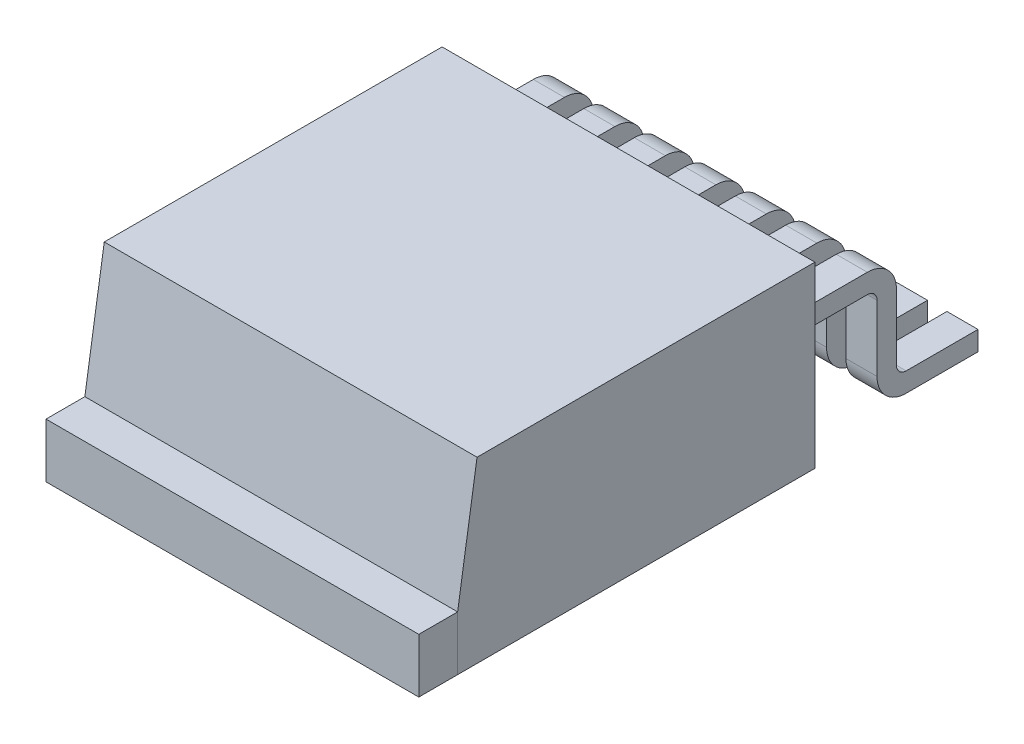
SolidWorks part; units mm, degrees
ref_plane "Front Plane" through (0, 0, 0) normal (0, 0, 1) x (1, 0, 0)
ref_plane "Top Plane" through (0, 0, 0) normal (0, 1, 0) x (1, 0, 0)
ref_plane "Right Plane" through (0, 0, 0) normal (1, 0, 0) x (0, 0, -1)
sketch "Sketch1" plane through (0, 0, 0) normal (1, 0, 0) x (0, 0, -1)
  line L0 (4.6, 0) -> (4.6, 4.6)
  line L1 (4.6, 4.6) -> (-4.1, 4.6)
  line L3 (-4.6, 0) -> (4.6, 0)
  line L4 (-4.1, 4.6) -> (-4.6, 1.4)
  line L5 (-4.6, 1.4) -> (-4.6, 0)
  dimension "D1" = 8.7
  dimension "D2" = 4.6
  dimension "D3" = 9.2
  dimension "D4" = 1.4
extrude "Boss-Extrude1" add sketch "Sketch1" along normal mid plane 9.6
sketch "Sketch2" plane through (0, 0, 4.6) normal (0, 0, 1) x (1, 0, 0)
  line L1 (4.8, 1.4) -> (-4.8, 1.4)
  line L2 (4.8, 1.4) -> (4.8, 0)
  line L3 (4.8, 0) -> (-4.8, 0)
  line L4 (-4.8, 1.4) -> (-4.8, 0)
extrude "Boss-Extrude2" add sketch "Sketch2" along normal blind 1 separate body
sketch "Sketch3" plane through (0, 0, -4.6) normal (0, 0, -1) x (-1, 0, 0)
  line L0 (-4.8, 4.6) -> (4.8, 4.6) construction
  line L1 (-4.3, 3.2) -> (-3.5, 3.2)
  line L2 (-4.3, 3.2) -> (-4.3, 2.7)
  line L3 (-4.3, 2.7) -> (-3.5, 2.7)
  line L4 (-3.5, 3.2) -> (-3.5, 2.7)
  line L5 (-4.8, 0) -> (-4.8, 4.6) construction
  dimension "D1" = 0.8
  dimension "D2" = 0.5
  dimension "D3" = 1.4
  dimension "D4" = 0.5
extrude "Boss-Extrude3" add sketch "Sketch3" along normal blind 2.6 separate body
sketch "Sketch4" plane through (0, 3.2, 0) normal (0, 1, 0) x (1, 0, 0)
  line L0 (3.5, 7.2) -> (3.5, 4.6) construction
  line L1 (4.3, 7.2) -> (3.5, 7.2)
  line L2 (4.3, 7.2) -> (4.3, 6.7)
  line L3 (4.3, 6.7) -> (3.5, 6.7)
  line L4 (3.5, 7.2) -> (3.5, 6.7)
  dimension "D1" = 0.5
extrude "Boss-Extrude4" add sketch "Sketch4" against normal up to surface (3.2 mm away) up to face at (0, 0, 0)
sketch "Sketch5" plane through (0, 0, -6.7) normal (0, 0, 1) x (1, 0, 0)
  line L0 (3.5, 0) -> (3.5, 2.7) construction
  line L1 (4.3, 0) -> (3.5, 0)
  line L2 (4.3, 0) -> (4.3, 0.5)
  line L3 (4.3, 0.5) -> (3.5, 0.5)
  line L4 (3.5, 0) -> (3.5, 0.5)
  dimension "D1" = 0.5
extrude "Boss-Extrude5" add sketch "Sketch5" against normal blind 2.6
fillet "Fillet1" radius 0.75 2 edges at (3.9, 3.2, -7.2) (3.9, 0, -6.7)
fillet "Fillet2" radius 0.25 2 edges at (3.9, 0.5, -7.2) (3.9, 2.7, -6.7)
pattern_linear "LPattern3" count 7 spacing 1.3 along (-1, 0, 0) of bodies 105
